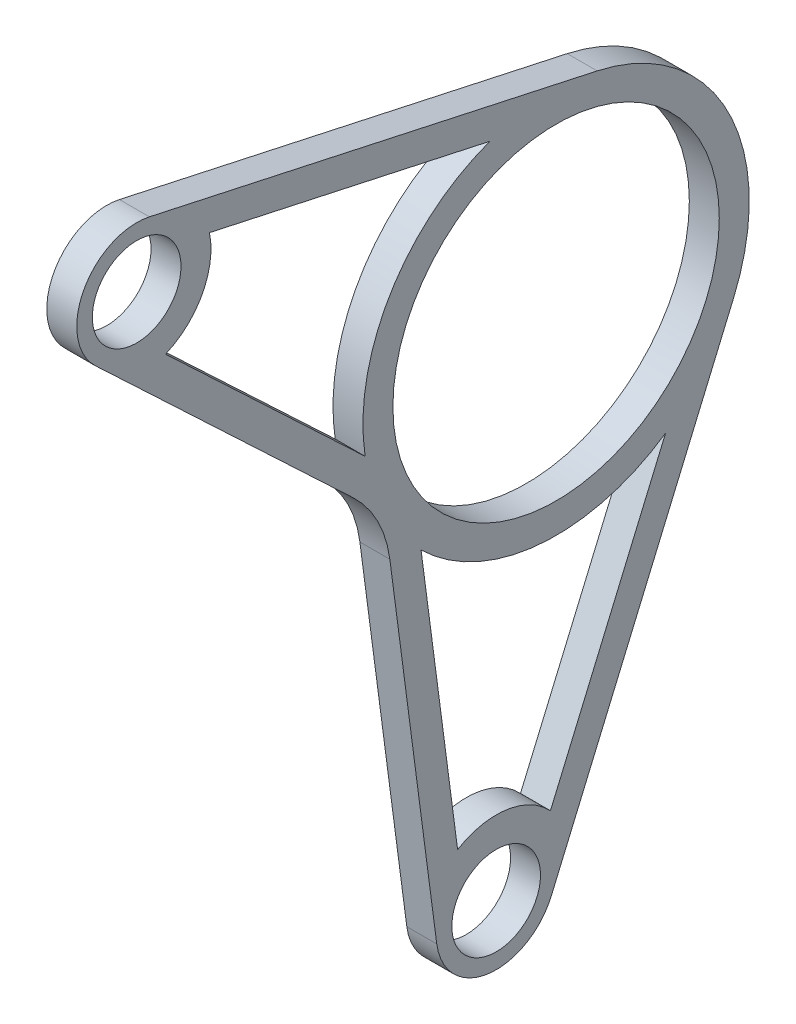
SolidWorks part; units mm, degrees
ref_plane "Front Plane" through (0, 0, 0) normal (0, 0, 1) x (1, 0, 0)
ref_plane "Top Plane" through (0, 0, 0) normal (0, 1, 0) x (1, 0, 0)
ref_plane "Right Plane" through (0, 0, 0) normal (1, 0, 0) x (0, 0, -1)
sketch "Sketch1" plane through (-101.6, 0, 0) normal (1, 0, 0) x (0, 0, -1)
  line L0 (279.4, 241.3) -> (266.7, 139.7) construction
  line L1 (190.5, 289.56) -> (279.4, 241.3) construction
  line L2 (279.4, 241.3) -> (266.7, 139.7)
  line L3 (190.5, 289.56) -> (279.4, 241.3)
  line L4 (181.7855, 280.3216) -> (242.9844, 222.5932)
  line L5 (242.9844, 222.5932) -> (254.1085, 138.0434)
  line L6 (278.3787, 134.7102) -> (317.0472, 225.2151)
  line L7 (288.1108, 281.302) -> (193.2022, 301.9692)
  line L8 (242.9844, 222.5932) -> (259.1168, 252.3109) construction
  line L9 (242.9844, 222.5932) -> (276.5374, 218.3991) construction
  line L10 (242.9844, 222.5932) -> (279.4, 241.3) construction
  line L11 (279.4, 241.3) -> (317.0472, 225.2151) construction
  circle A0 centre (190.5, 289.56) radius 9.398
  circle A1 centre (279.4, 241.3) radius 34.5894
  circle A2 centre (266.7, 139.7) radius 9.398
  arc A3 (193.2022, 301.9692) -> (181.7855, 280.3216) centre (190.5, 289.56) ccw
  arc A5 (288.1108, 281.302) -> (317.0472, 225.2151) centre (279.4, 241.3) cw
  arc A6 (254.1085, 138.0434) -> (278.3787, 134.7102) centre (266.7, 139.7) ccw
  dimension "D1" = 18.796
  dimension "D2" = 69.1789
  dimension "D4" = 12.7
  dimension "D3" = 6.35
extrude "Boss-Extrude1" add sketch "Sketch1" along normal mid plane 6.35
fillet "Fillet1" radius 25.4 1 edges at (-101.6, 222.5932, -242.9844)
sketch "Sketch2" plane through (-98.425, 0, 0) normal (1, 0, 0) x (0, 0, -1)
  line L0 (279.4, 241.3) -> (266.7, 139.7) construction
  line L1 (190.5, 289.56) -> (279.4, 241.3) construction
  line L2 (279.4, 241.3) -> (266.7, 139.7) construction
  line L3 (190.5, 289.56) -> (279.4, 241.3) construction
  line L4 (181.7855, 280.3216) -> (242.9844, 222.5932)
  line L5 (242.9844, 222.5932) -> (254.1085, 138.0434)
  line L6 (278.3787, 134.7102) -> (317.0472, 225.2151)
  line L7 (288.1108, 281.302) -> (193.2022, 301.9692)
  line L8 (181.7855, 280.3216) -> (242.9844, 222.5932) construction
  line L9 (242.9844, 222.5932) -> (254.1085, 138.0434) construction
  line L10 (278.3787, 134.7102) -> (317.0472, 225.2151) construction
  line L11 (288.1108, 281.302) -> (193.2022, 301.9692) construction
  line L12 (196.6258, 275.0523) -> (238.9248, 235.1519)
  line L13 (265.3612, 279.7571) -> (205.9321, 292.6983)
  line L14 (250.7793, 212.0273) -> (258.5244, 153.1595)
  line L15 (278.2014, 150.4572) -> (302.6035, 207.5711)
  arc A0 (205.9321, 292.6983) -> (196.6258, 275.0523) centre (190.5, 289.56) cw
  circle A1 centre (266.7, 139.7) radius 9.398
  circle A2 centre (266.7, 139.7) radius 9.398 construction
  circle A3 centre (279.4, 241.3) radius 34.5894
  circle A4 centre (279.4, 241.3) radius 34.5894 construction
  circle A5 centre (190.5, 289.56) radius 9.398
  circle A6 centre (190.5, 289.56) radius 9.398 construction
  arc A7 (265.3612, 279.7571) -> (238.9248, 235.1519) centre (279.4, 241.3) ccw
  arc A8 (250.7793, 212.0273) -> (302.6035, 207.5711) centre (279.4, 241.3) ccw
  arc A9 (254.1085, 138.0434) -> (278.3787, 134.7102) centre (266.7, 139.7) ccw
  arc A10 (317.0472, 225.2151) -> (288.1108, 281.302) centre (279.4, 241.3) ccw
  arc A11 (193.2022, 301.9692) -> (181.7855, 280.3216) centre (190.5, 289.56) ccw
  arc A12 (254.1085, 138.0434) -> (278.3787, 134.7102) centre (266.7, 139.7) ccw construction
  arc A13 (317.0472, 225.2151) -> (288.1108, 281.302) centre (279.4, 241.3) ccw construction
  arc A14 (193.2022, 301.9692) -> (181.7855, 280.3216) centre (190.5, 289.56) ccw construction
  arc A15 (258.5244, 153.1595) -> (278.2014, 150.4572) centre (266.7, 139.7) cw
  dimension "D5" = 6.35
  dimension "D6" = 6.35
  dimension "D7" = 6.35
  dimension "D8" = 6.35
  dimension "D9" = 6.35
  dimension "D10" = 6.35
  dimension "D11" = 6.35
  dimension "D12" = 6.35
  dimension "D1" = 0
  dimension "D2" = 0
  dimension "D3" = 0
  dimension "D4" = 0
extrude "Cut-Extrude1" cut sketch "Sketch2" against normal through all
equation "\"strunt-width\"= 0.25in"
equation "\"D6@Sketch2\"=\"strunt-width\""
equation "\"D5@Sketch2\"=\"strunt-width\""
equation "\"D7@Sketch2\"=\"strunt-width\""
equation "\"D8@Sketch2\"=\"strunt-width\""
equation "\"D9@Sketch2\"=\"strunt-width\""
equation "\"D10@Sketch2\"=\"strunt-width\""
equation "\"D11@Sketch2\"=\"strunt-width\""
equation "\"D12@Sketch2\"=\"strunt-width\""
equation "\"D3@Sketch1\"=\"strunt-width\""
